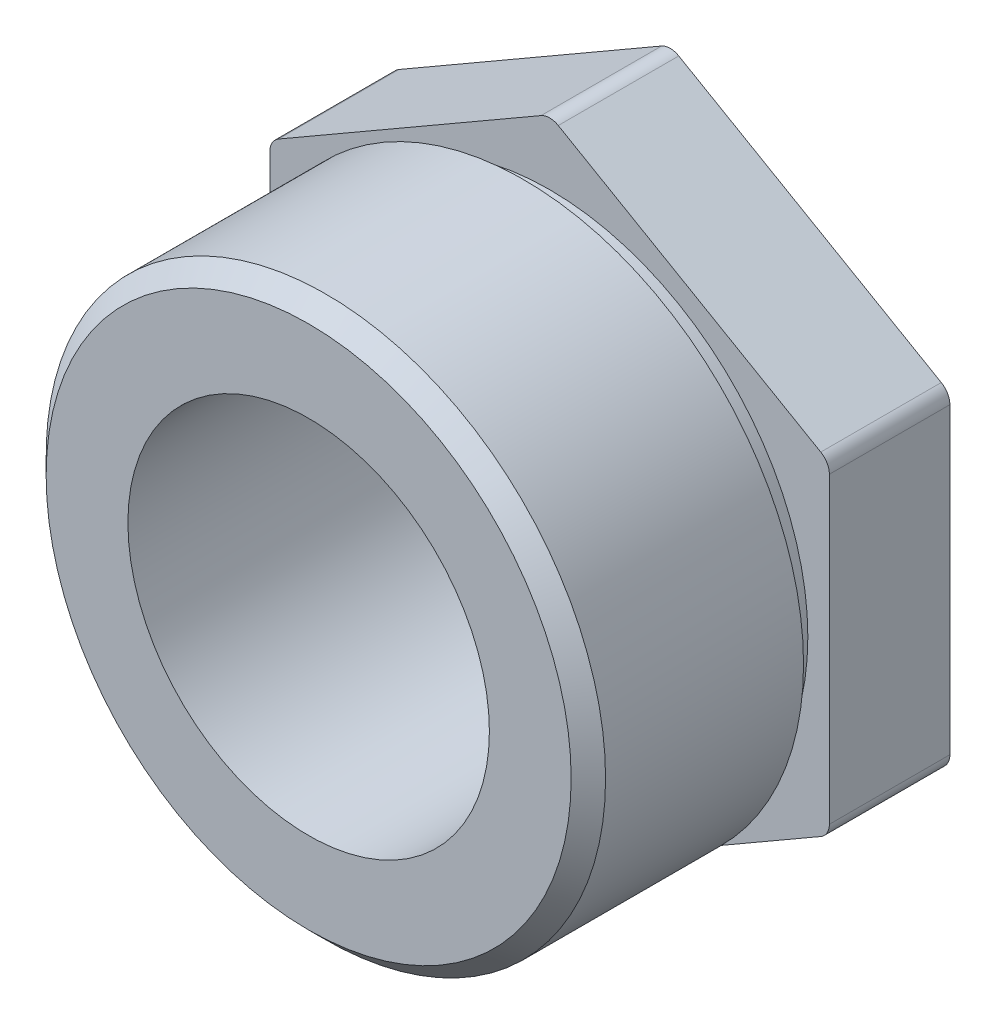
SolidWorks part; units mm, degrees
ref_plane "Front Plane" through (0, 0, 0) normal (0, 0, 1) x (1, 0, 0)
ref_plane "Top Plane" through (0, 0, 0) normal (0, 1, 0) x (1, 0, 0)
ref_plane "Right Plane" through (0, 0, 0) normal (1, 0, 0) x (0, 0, -1)
sketch "Sketch1" plane through (0, 0, 0) normal (0, 0, 1) x (1, 0, 0)
  circle A0 centre (0, 0) radius 32.5
  dimension "D1" = 65
extrude "Boss-Extrude1" add sketch "Sketch1" along normal blind 42
cosmetic thread "Cosmetic Thread1" parameters "D1"=25, "D2"=59.61
sketch "Sketch2" plane through (0, 0, 42) normal (0, 0, 1) x (1, 0, 0)
  circle A0 centre (0, 0) radius 30
  circle A1 centre (0, 0) radius 32.5
  circle A2 centre (0, 0) radius 32.5
  dimension "D2" = 60
  dimension "D1" = 0
extrude "Cut-Extrude1" cut sketch "Sketch2" along normal blind 3 from offset 28 offset against normal yes
sketch "Sketch3" plane through (0, 0, 0) normal (0, 0, -1) x (-1, 0, 0)
  line L1 (0, 37.5278) -> (-32.5, 18.7639)
  line L2 (-32.5, 18.7639) -> (-32.5, -18.7639)
  line L3 (-32.5, -18.7639) -> (0, -37.5278)
  line L4 (0, -37.5278) -> (32.5, -18.7639)
  line L5 (32.5, -18.7639) -> (32.5, 18.7639)
  line L6 (32.5, 18.7639) -> (0, 37.5278)
  circle A0 centre (0, 0) radius 32.5 construction
  circle A1 centre (0, 0) radius 32.5 construction
extrude "Boss-Extrude2" add sketch "Sketch3" against normal blind 14
fillet "Fillet1" radius 2 6 edges at (32.5, -18.7639, 7) (0, -37.5278, 7) (-32.5, -18.7639, 7) (-32.5, 18.7639, 7) (0, 37.5278, 7) (32.5, 18.7639, 7)
chamfer "Chamfer1" distance 2 angle 45 1 edges at (32.5, 0, 42)
sketch "Sketch4" plane through (0, 0, 42) normal (0, 0, 1) x (1, 0, 0)
  circle A0 centre (0, 0) radius 21
  dimension "D1" = 42
extrude "Cut-Extrude2" cut sketch "Sketch4" against normal through all
